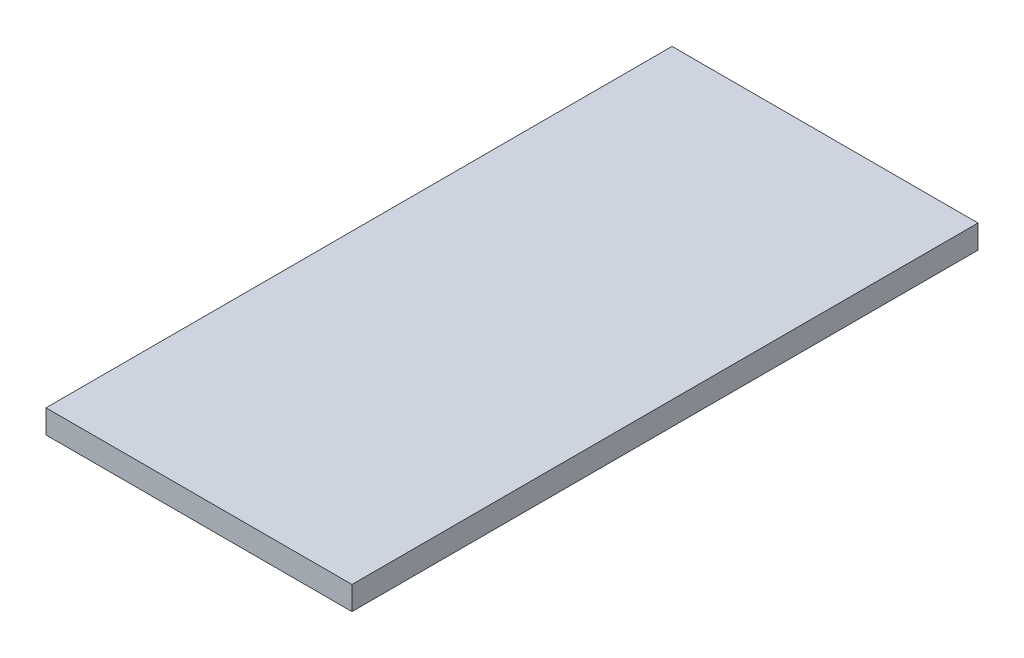
SolidWorks part; units mm, degrees
ref_plane "Plane1" through (0, 0, 0) normal (0, 0, 1) x (1, 0, 0)
ref_plane "Plane2" through (0, 0, 0) normal (0, 1, 0) x (1, 0, 0)
ref_plane "Plane3" through (0, 0, 0) normal (1, 0, 0) x (0, 0, -1)
sketch "Sketch1" plane through (0, 0, 0) normal (0, 1, 0) x (1, 0, 0)
  line L1 (0, 0) -> (130, 0)
  line L2 (0, 0) -> (0, 266)
  line L3 (0, 266) -> (130, 266)
  line L4 (130, 0) -> (130, 266)
  dimension "D1" = 266
  dimension "D2" = 130
extrude "Boss-Extrude1" add sketch "Sketch1" along normal blind 10
